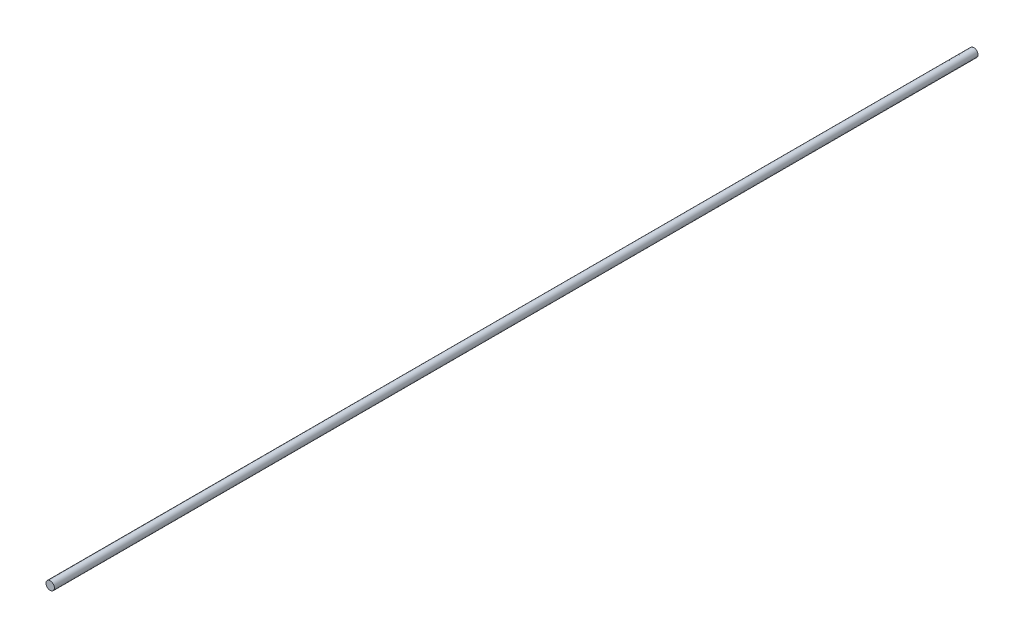
SolidWorks part; units mm, degrees
ref_plane "前视基准面" through (0, 0, 0) normal (0, 0, 1) x (1, 0, 0)
ref_plane "上视基准面" through (0, 0, 0) normal (0, 1, 0) x (1, 0, 0)
ref_plane "右视基准面" through (0, 0, 0) normal (1, 0, 0) x (0, 0, -1)
sketch "草图1" plane through (0, 0, 0) normal (0, 0, 1) x (1, 0, 0)
  circle A0 centre (0, 0) radius 0.5
  dimension "D1" = 1
extrude "凸台-拉伸1" add sketch "草图1" along normal blind 110
